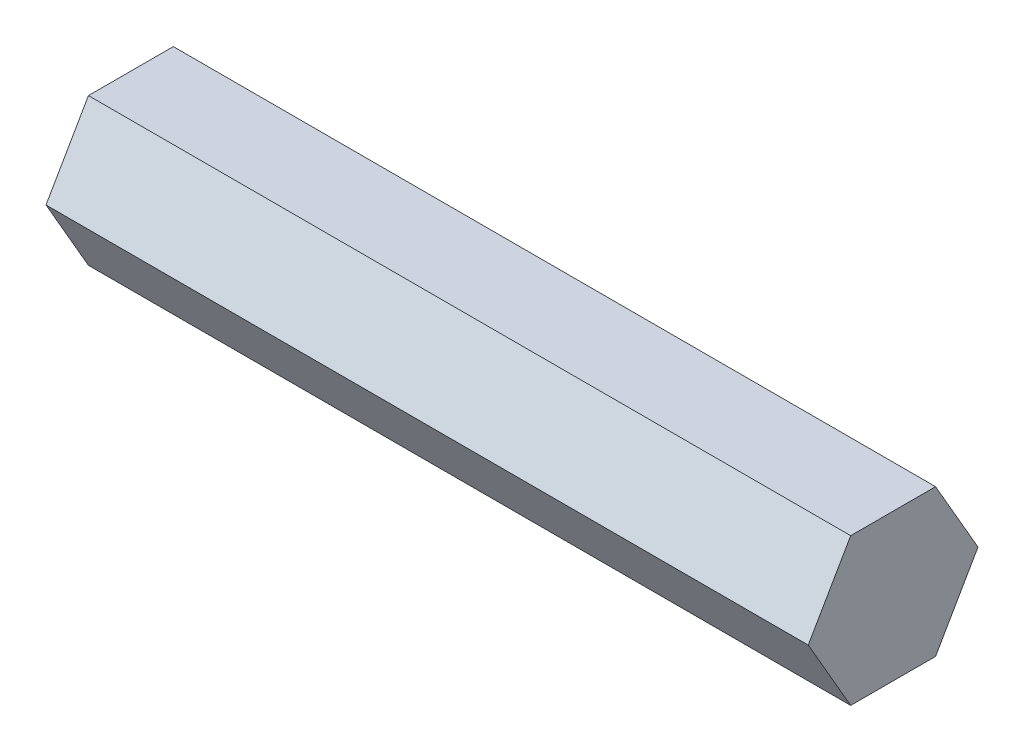
SolidWorks part; units mm, degrees
ref_plane "Front Plane" through (0, 0, 0) normal (0, 0, 1) x (1, 0, 0)
ref_plane "Top Plane" through (0, 0, 0) normal (0, 1, 0) x (1, 0, 0)
ref_plane "Right Plane" through (0, 0, 0) normal (1, 0, 0) x (0, 0, -1)
sketch "Sketch1" plane through (0, 0, 0) normal (1, 0, 0) x (0, 0, -1)
  line L1 (7.3323, 0) -> (3.6662, 6.35)
  line L2 (3.6662, 6.35) -> (-3.6662, 6.35)
  line L3 (-3.6662, 6.35) -> (-7.3323, 0)
  line L4 (-7.3323, 0) -> (-3.6662, -6.35)
  line L5 (-3.6662, -6.35) -> (3.6662, -6.35)
  line L6 (3.6662, -6.35) -> (7.3323, 0)
  circle A0 centre (0, 0) radius 6.35 construction
  dimension "D1" = 12.7
extrude "Boss-Extrude1" add sketch "Sketch1" along normal blind 65.85
